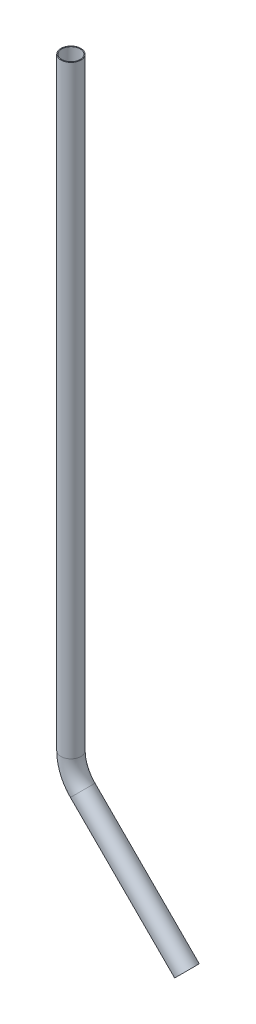
SolidWorks part; units mm, degrees
ref_plane "Front Plane" through (0, 0, 0) normal (0, 0, 1) x (1, 0, 0)
ref_plane "Top Plane" through (0, 0, 0) normal (0, 1, 0) x (1, 0, 0)
ref_plane "Right Plane" through (0, 0, 0) normal (1, 0, 0) x (0, 0, -1)
sketch "Sketch1" plane through (0, 0, 0) normal (0, 0, 1) x (1, 0, 0)
  line L0 (21.59, -253.638) -> (21.59, -196.488) construction
  line L2 (21.59, -196.488) -> (-111.76, -196.488) construction
  line L5 (21.59, -196.488) -> (-111.76, -63.138) construction
  line L7 (-1.818, -173.0801) -> (-100.6008, -74.2973)
  line L8 (-111.76, -47.3565) -> (-111.76, 524.1435)
  arc A1 (-111.76, -47.3565) -> (-100.6008, -74.2973) centre (-73.66, -47.3565) ccw
  dimension "D5" = 139.7
  dimension "D6" = 38.1
  dimension "D1" = 571.5
  dimension "D2" = 45
  dimension "D3" = 57.15
  dimension "D4" = 133.35
sketch "Sketch2" plane through (0, 0, 0) normal (0, 1, 0) x (1, 0, 0)
  circle A1 centre (-111.76, 0) radius 9.525
  circle A2 centre (-111.76, 0) radius 8.7122
  dimension "D1" = 19.05
  dimension "D2" = 0.8128
sweep "Sweep1" add profiles "Sketch2" path "Sketch1"
